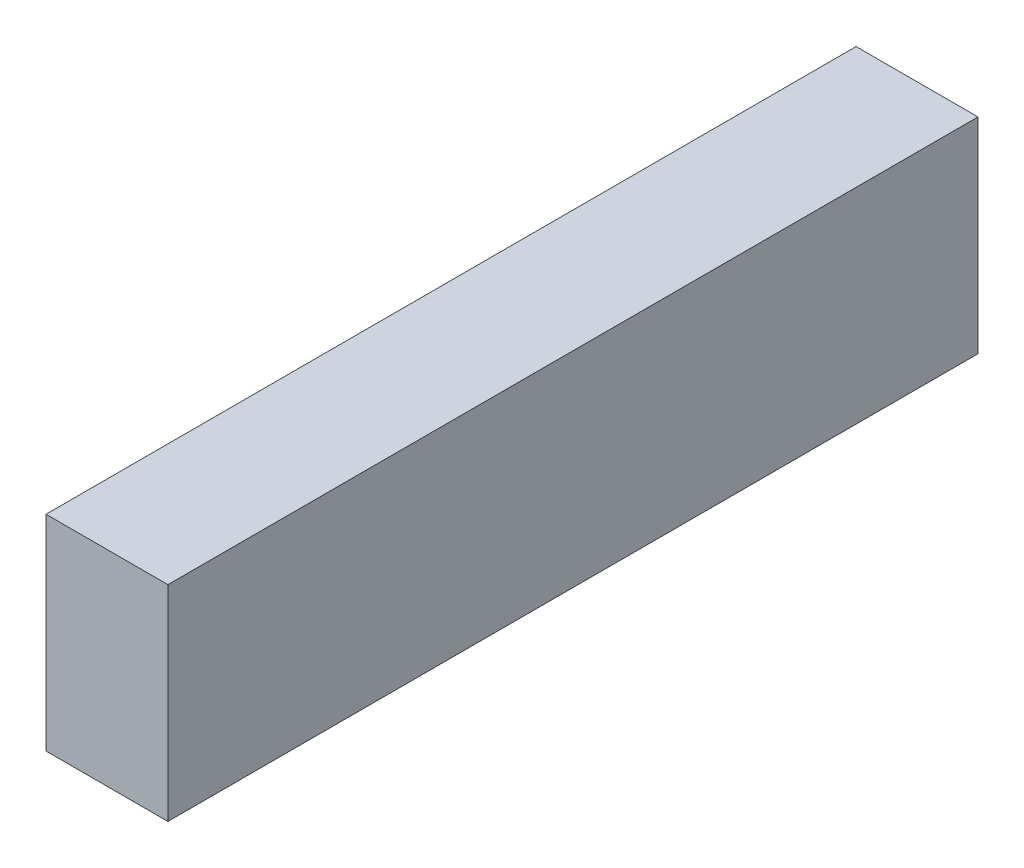
SolidWorks part; units mm, degrees
ref_plane "Front Plane" through (0, 0, 0) normal (0, 0, 1) x (1, 0, 0)
ref_plane "Top Plane" through (0, 0, 0) normal (0, 1, 0) x (1, 0, 0)
ref_plane "Right Plane" through (0, 0, 0) normal (1, 0, 0) x (0, 0, -1)
sketch "Sketch1" plane through (0, 0, 0) normal (0, 0, 1) x (1, 0, 0)
  line L0 (0, 0) -> (11.89, 0)
  line L1 (11.89, 0) -> (11.89, 20)
  line L2 (11.89, 20) -> (0, 20)
  line L3 (0, 20) -> (0, 0)
  dimension "D1" = 20
  dimension "D2" = 11.89
extrude "Boss-Extrude1" add sketch "Sketch1" along normal blind 79
sketch "Sketch4" plane through (0, 0, 0) normal (-1, 0, 0) x (0, 0, 1)
  line L0 (39.5, 0) -> (39.5, 20) construction
  line L1 (0, 20) -> (79, 20) construction
  line L2 (0, 0) -> (79, 0) construction
  circle A0 centre (39.5, 10) radius 2.15
  circle A1 centre (9.5, 10) radius 2.15
  circle A2 centre (69.5, 10) radius 2.15
  point P5 (39.5, 10)
  point P9 (39.5, 20)
  point P18 (39.5, 0)
  dimension "D1" = 4.3
  dimension "D2" = 30
  dimension "D3" = 30
extrude "Cut-Extrude1" cut sketch "Sketch4" against normal blind 6.82
sketch "Sketch5" plane through (0, 0, 0) normal (0, -1, 0) x (1, 0, 0)
  line L0 (0, 39.5) -> (11.89, 39.5) construction
  line L1 (0, 79) -> (0, 0) construction
  line L2 (11.89, 79) -> (11.89, 0) construction
  line L3 (5.945, 0) -> (5.945, 79) construction
  line L4 (0, 0) -> (11.89, 0) construction
  line L5 (0, 79) -> (11.89, 79) construction
  circle A0 centre (5.945, 39.5) radius 2.15
  circle A1 centre (5.945, 69.5) radius 2.15
  circle A2 centre (5.945, 9.5) radius 2.15
  dimension "D1" = 4.3
  dimension "D2" = 30
  dimension "D3" = 30
extrude "Cut-Extrude2" cut sketch "Sketch5" against normal blind 6.825
